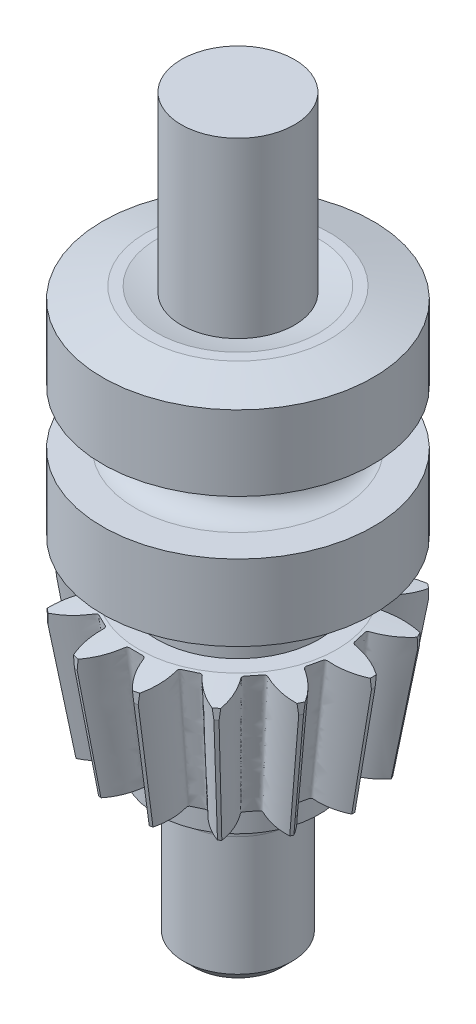
SolidWorks part; units mm, degrees
ref_plane "Front Plane" through (0, 0, 0) normal (0, 0, 1) x (1, 0, 0)
ref_plane "Top Plane" through (0, 0, 0) normal (0, 1, 0) x (1, 0, 0)
ref_plane "Right Plane" through (0, 0, 0) normal (1, 0, 0) x (0, 0, -1)
sketch "Sketch1" plane through (0, 0, 0) normal (0, 0, 1) x (1, 0, 0)
  line L0 (0, 0) -> (0, -75.1876) construction
  line L1 (0, 0) -> (9.1333, 0)
  line L2 (0, 0) -> (0, -11.9144)
  line L3 (0, -11.9144) -> (7.686, -11.9144)
  line L4 (0, -75.1876) -> (10.5, -0.1913) construction
  line L5 (9.1333, 0) -> (12.6589, -0.4936)
  line L6 (0, -75.1876) -> (12.6589, -0.4936) construction
  line L7 (0, -75.1876) -> (9.1333, 0) construction
  line L8 (12.6589, -0.4936) -> (10.653, -12.3298)
  line L9 (10.653, -12.3298) -> (7.686, -11.9144)
  line L11 (10.5, -0.1913) -> (0, -0.1913) construction
  dimension "D1" = 2.18
  dimension "D2" = 10.5
  dimension "D3" = 1.38
  dimension "D4" = 12
  dimension "D5" = 7.97
  dimension "D6" = 7.686
  dimension "D7" = 75.1876
  dimension "D8" = 75.7278
  dimension "D9" = 1.649
revolve "Revolve1" add sketch "Sketch1" angle 360 about L0
ref_plane "Plane1" through (0, 1.2541, 0.1756) normal (0, 0.9903, 0.1387) x (1, 0, 0)
ref_plane "Plane2" through (0, -73.785, -10.3304) normal (0, 0.9903, 0.1387) x (1, 0, 0)
sketch "Sketch2" plane through (0, 1.2541, 0.1756) normal (0, 0.9903, 0.1387) x (1, 0, 0)
  line L0 (0, 4.5573) -> (133.355, -837.4128) construction
  line L1 (0, 4.5573) -> (75.4188, -932.497) construction
  line L2 (0, -170.139) -> (0, 4.5573) construction
  line L3 (-67.5504, -12.6051) -> (67.5504, -12.6051) construction
  line L4 (2.3465, -10.258) -> (1.1998, -10.3503) construction
  arc A0 (-3.0757, -12.676) -> (3.0757, -12.676) centre (0, 4.5573) ccw
  arc A1 (-0.6074, -9.3088) -> (0.6074, -9.3088) centre (0, 4.5573) ccw
  circle A2 centre (0, 4.5573) radius 15 construction
  circle A3 centre (0, 4.5573) radius 14.0954 construction
  arc A4 (0.8919, -9.5138) -> (0.6074, -9.3088) centre (0.6198, -9.5915) ccw
  arc A5 (0.8919, -9.5138) -> (3.0757, -12.676) centre (6.6609, -7.865) ccw
  arc A6 (-3.0757, -12.676) -> (-0.8919, -9.5138) centre (-6.6609, -7.865) ccw
  arc A7 (-0.6074, -9.3088) -> (-0.8919, -9.5138) centre (-0.6198, -9.5915) ccw
  ellipse E7 centre (0, -0.0684) end of major axis (12.6589, -0.0684) minor radius 12.5367 construction
  point P21 (0, -12.6051)
  dimension "D2" = 35.0113
  dimension "D3" = 27.7588
  dimension "D4" = 30
  dimension "D5" = 28.1908
  dimension "D8" = 6
  dimension "D9" = 0.283
  dimension "D1" = 17.1624
  dimension "D6" = 9
  dimension "D7" = 1.1504
sketch "Sketch3" plane through (0, -73.785, -10.3304) normal (0, 0.9903, 0.1387) x (1, 0, 0)
  line L0 (0, -12.6051) -> (0, 0) construction
  line L1 (21.082, -9.0451) -> (-20.32, -9.0451) construction
  line L2 (0, -170.139) -> (0, 4.5573) construction
  circle A0 centre (0, -10.4281) radius 0.0127
  ellipse E0 centre (0, 0) end of major axis (9.1333, 0) minor radius 9.0451 construction
  ellipse E1 centre (0, -0.0684) end of major axis (12.6589, -0.0684) minor radius 12.5367 construction
  dimension "D2" = 0.0254
  dimension "D1" = 1.383
loft "Cut-Loft1" cut profiles "Sketch3", "Sketch2"
pattern_circular "CirPattern2" count 14 every 25.714 about axis through (0, 0, 0) along (0, -1, 0) of "Cut-Loft1"
sketch "Sketch5" plane through (0, 0, 0) normal (0, 0, 1) x (1, 0, 0)
  line L0 (0, 13.8442) -> (0, -28)
  line L1 (0, 25.41) -> (0, 23.5) construction
  line L3 (4.6, 16.5) -> (0, 13.8442)
  line L4 (4.6, 16.5) -> (0, 16.5) construction
  line L5 (0, 13.8442) -> (0, 16.5) construction
  line L6 (0, 16.5) -> (0, 23.5) construction
  line L7 (4.6, 16.5) -> (4.6, 23.872)
  line L8 (9.5, 16.5) -> (4.6, 16.5) construction
  line L14 (0, 0) -> (0, 25.41) construction
  line L15 (7.5, 24.5) -> (8.5, 24.5)
  line L16 (8.5, 24.5) -> (12.5, 23.4282)
  line L17 (12.5, 23.4282) -> (12.5, 16.5)
  line L18 (12.5, 16.5) -> (9.5, 16.5)
  line L19 (7.5, 14.5) -> (7.5, 13.5)
  line L20 (9.5, 11.5) -> (12.5, 11.5)
  line L21 (12.5, 11.5) -> (12.5, 4.5)
  line L22 (12.5, 4.5) -> (9.5, 4.5)
  line L23 (7.5, 2.5) -> (7.5, 0)
  line L24 (0, 0) -> (9.1333, 0) construction
  line L25 (12.6589, -0.4936) -> (0, -0.4936) construction
  line L26 (0, 0) -> (0, -11.9144) construction
  line L27 (0, 0) -> (0, -28) construction
  line L28 (0, 0) -> (0, -75.1876) construction
  line L29 (0, -28) -> (5, -28)
  line L31 (5, -28) -> (5, -16)
  line L32 (7, -14) -> (7.5, -14)
  line L33 (7.5, -14) -> (7.5, 0)
  arc A0 (7.5, 24.5) -> (4.6, 23.872) centre (0, 52.125) cw
  arc A1 (4.6, 23.872) -> (0, 23.5) centre (0, 52.125) cw construction
  arc A4 (9.5, 16.5) -> (7.5, 14.5) centre (9.5, 14.5) ccw
  arc A5 (7.5, 13.5) -> (9.5, 11.5) centre (9.5, 13.5) ccw
  arc A6 (9.5, 4.5) -> (7.5, 2.5) centre (9.5, 2.5) ccw
  arc A7 (5, -16) -> (7, -14) centre (7, -16) cw
  point P0 (4.5667, 0)
  point P36 (12.5, 19.9641)
  point P58 (7.5, 16.5)
  point P61 (7.5, 11.5)
  dimension "D21" = 2
  dimension "D22" = 9.2
  dimension "D3" = 20
  dimension "D4" = 4.5
  dimension "D5" = 28
  dimension "D6" = 7.5
  dimension "D7" = 24.5
  dimension "D8" = 25
  dimension "D9" = 15
  dimension "D10" = 8
  dimension "D11" = 7
  dimension "D12" = 15
  dimension "D13" = 5
  dimension "D14" = 4
  dimension "D15" = 25.3179
  dimension "D16" = 1
  dimension "D17" = 60
  dimension "D18" = 10
  dimension "D20" = 14
revolve "Revolve2" add sketch "Sketch5" angle 360 about L0
sketch "Sketch6" plane through (0, 24.5, 0) normal (0, 1, 0) x (1, 0, 0)
  line L1 (-4.6, -4.6) -> (4.6, -4.6)
  line L2 (-4.6, -4.6) -> (-4.6, 4.6)
  line L3 (-4.6, 4.6) -> (4.6, 4.6)
  line L4 (4.6, -4.6) -> (4.6, 4.6)
  line L5 (-4.6, -4.6) -> (4.6, 4.6) construction
  line L6 (-4.6, 4.6) -> (4.6, -4.6) construction
  circle A0 centre (0, 0) radius 4.6 construction
  point P0 (0, 0)
sketch "Sketch7" plane through (0, 0, 0) normal (0, 1, 0) x (1, 0, 0)
  circle A0 centre (0, 0) radius 12.5 construction
  circle A1 centre (0, 0) radius 12.5
extrude "Cut-Extrude2" cut sketch "Sketch7" against normal blind 3 flip side to cut
chamfer "Chamfer1" distance 1 angle 45 1 edges at (-5, -28, 0)
sketch "Sketch8" plane through (0, 0, 0) normal (0, 1, 0) x (1, 0, 0)
  line L1 (-33.5203, -41.9848) -> (24.4416, -41.9848)
  line L2 (-33.5203, -41.9848) -> (-33.5203, 44.1028)
  line L3 (-33.5203, 44.1028) -> (24.4416, 44.1028)
  line L4 (24.4416, -41.9848) -> (24.4416, 44.1028)
extrude "Cut-Extrude3" [suppressed] cut sketch "Sketch8" along normal through all
sketch "Sketch9" plane through (0, -28, 0) normal (0, -1, 0) x (1, 0, 0)
  line L1 (12.1979, 21.6415) -> (-10.7063, 21.6415)
  line L2 (12.1979, 21.6415) -> (12.1979, -17.7509)
  line L3 (12.1979, -17.7509) -> (-10.7063, -17.7509)
  line L4 (-10.7063, 21.6415) -> (-10.7063, -17.7509)
extrude "Cut-Extrude4" [suppressed] cut sketch "Sketch9" against normal up to surface (14 mm away)
sketch "Sketch10" plane through (0, 0, 0) normal (0, 1, 0) x (1, 0, 0)
  circle A0 centre (0, 0) radius 5.2225
extrude "Boss-Extrude1" add sketch "Sketch10" along normal blind 40
